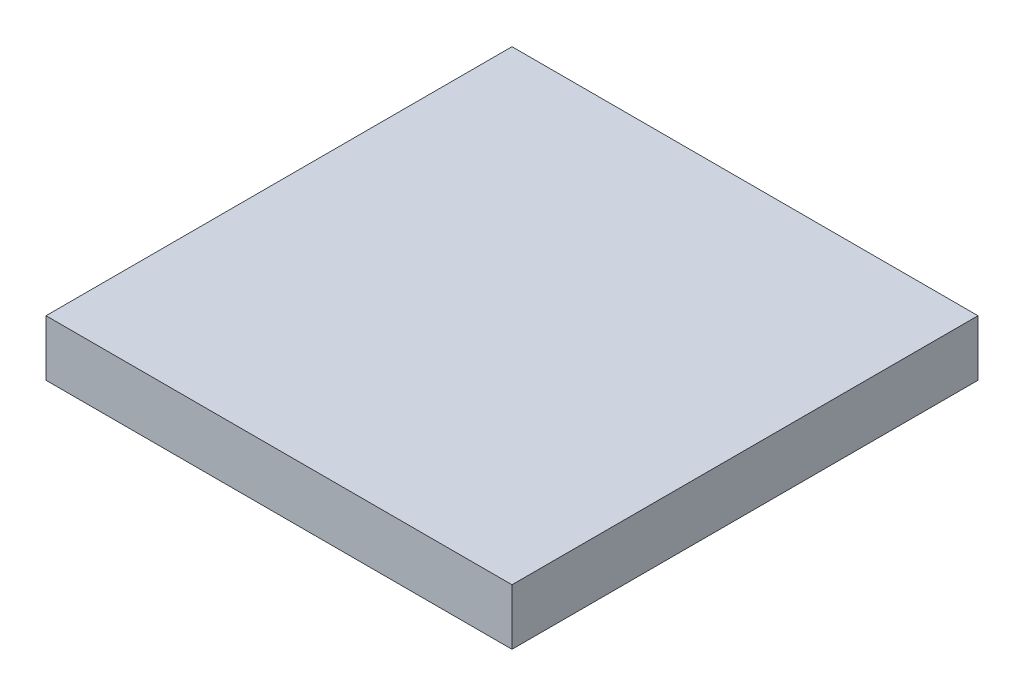
SolidWorks part; units mm, degrees
ref_plane "Front Plane" through (0, 0, 0) normal (0, 0, 1) x (1, 0, 0)
ref_plane "Top Plane" through (0, 0, 0) normal (0, 1, 0) x (1, 0, 0)
ref_plane "Right Plane" through (0, 0, 0) normal (1, 0, 0) x (0, 0, -1)
sketch "Sketch1" plane through (0, 0, 0) normal (0, 1, 0) x (1, 0, 0)
  line L1 (-12.5, -12.5) -> (12.5, -12.5)
  line L2 (-12.5, -12.5) -> (-12.5, 12.5)
  line L3 (-12.5, 12.5) -> (12.5, 12.5)
  line L4 (12.5, -12.5) -> (12.5, 12.5)
  line L5 (-12.5, -12.5) -> (12.5, 12.5) construction
  line L6 (-12.5, 12.5) -> (12.5, -12.5) construction
  point P0 (0, 0)
  dimension "D1" = 25
  dimension "D2" = 25
extrude "Boss-Extrude1" add sketch "Sketch1" along normal blind 3
sketch "Sketch2" plane through (0, 0, 0) normal (0, -1, 0) x (1, 0, 0)
  circle A0 centre (0, 0) radius 10
  circle A1 centre (0, 0) radius 5
  dimension "D1" = 10
  dimension "D2" = 20
extrude "Cut-Extrude1" cut sketch "Sketch2" against normal blind 2
sketch "Sketch3" plane through (0, 0, 0) normal (0, -1, 0) x (1, 0, 0)
  line L0 (-12.5, 12.5) -> (12.5, 12.5) construction
  line L1 (-12.5, -12.5) -> (-12.5, 12.5) construction
  line L2 (12.5, -12.5) -> (-12.5, -12.5) construction
  line L3 (12.5, 12.5) -> (12.5, -12.5) construction
  circle A0 centre (-10.5, 10.5) radius 1.25
  circle A1 centre (10.5, 10.5) radius 1.25
  circle A2 centre (10.5, -10.5) radius 1.25
  circle A3 centre (-10.5, -10.5) radius 1.25
  dimension "D1" = 2.5
  dimension "D4" = 2.5
  dimension "D7" = 2.5
  dimension "D10" = 2.5
  dimension "D2" = 2
  dimension "D3" = 2
  dimension "D5" = 2
  dimension "D6" = 2
  dimension "D8" = 2
  dimension "D9" = 2
  dimension "D11" = 2
  dimension "D12" = 2
extrude "Cut-Extrude2" cut sketch "Sketch3" against normal blind 2
